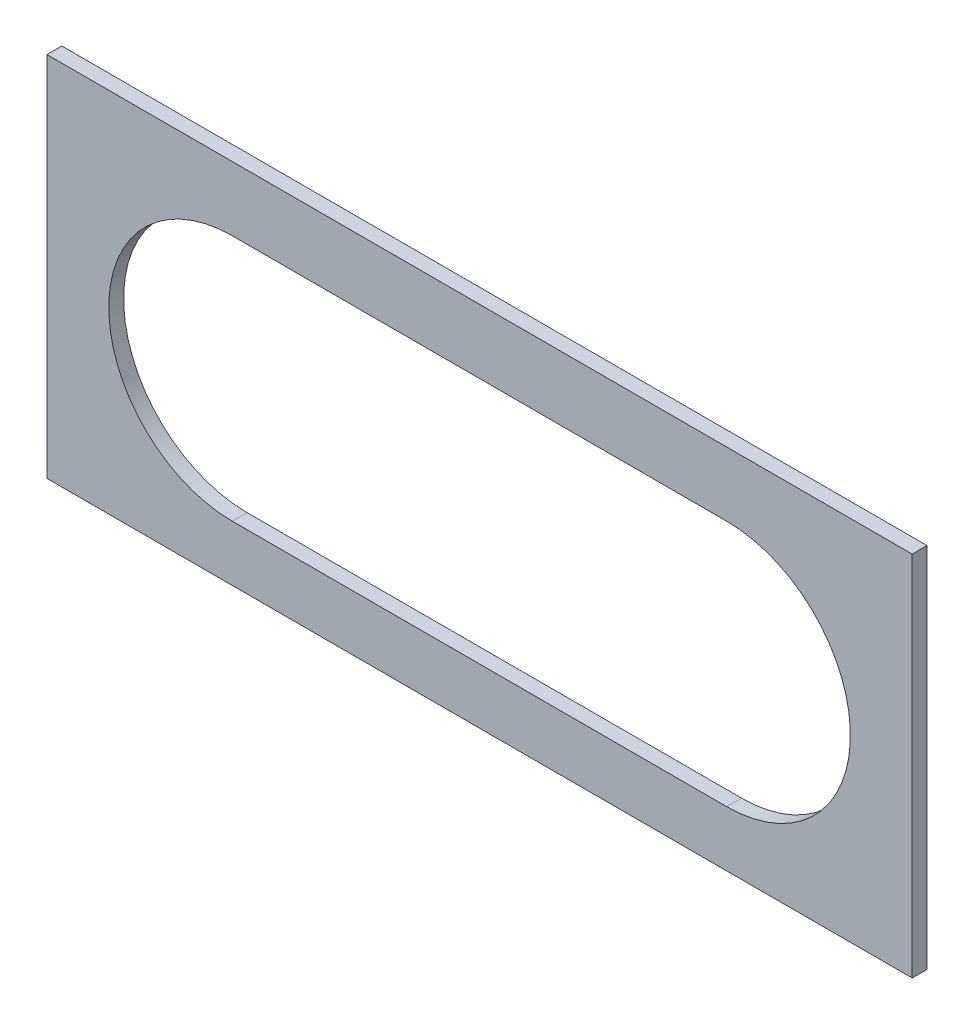
SolidWorks part; units mm, degrees
ref_plane "Plan de face" through (0, 0, 0) normal (0, 0, 1) x (1, 0, 0)
ref_plane "Plan de dessus" through (0, 0, 0) normal (0, 1, 0) x (1, 0, 0)
ref_plane "Plan de droite" through (0, 0, 0) normal (1, 0, 0) x (0, 0, -1)
sketch "Esquisse1" plane through (0, 0, 0) normal (0, 0, 1) x (1, 0, 0)
  line L0 (-350, -3.5) -> (350, -3.5) construction
  line L1 (-350, 148.5) -> (350, 148.5)
  line L2 (-350, 148.5) -> (-350, -148.5)
  line L3 (-350, -148.5) -> (350, -148.5)
  line L4 (350, 148.5) -> (350, -148.5)
  line L5 (-350, 148.5) -> (350, -148.5) construction
  line L6 (-350, -148.5) -> (350, 148.5) construction
  line L7 (-200, 96.5) -> (200, 96.5)
  line L8 (-200, -103.5) -> (200, -103.5)
  arc A0 (-200, 96.5) -> (-200, -103.5) centre (-200, -3.5) ccw
  arc A1 (200, -103.5) -> (200, 96.5) centre (200, -3.5) ccw
  point P0 (0, 0)
  dimension "D4" = 150
  dimension "D6" = 200
  dimension "D7" = 200
  dimension "D1" = 700
  dimension "D2" = 297
  dimension "D3" = 145
  dimension "D5" = 150
extrude "Boss.-Extru.1" add sketch "Esquisse1" along normal blind 12
